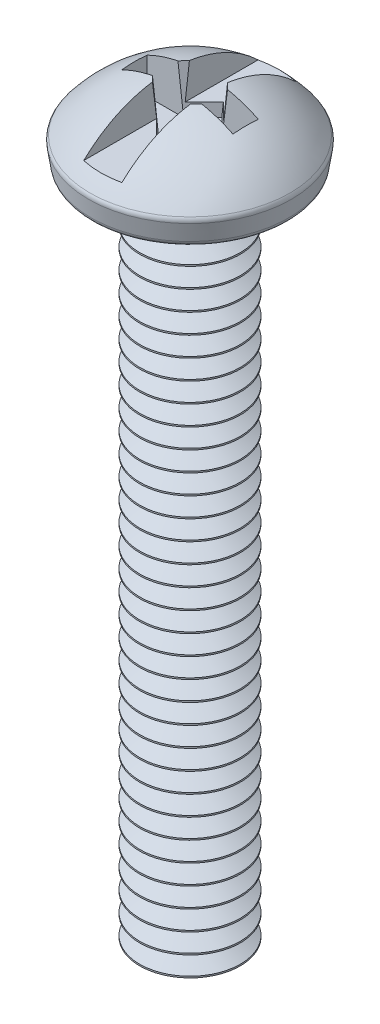
SolidWorks part; units mm, degrees
material "Plain Carbon Steel"
ref_plane "Front Plane" through (0, 0, 0) normal (0, 0, 1) x (1, 0, 0)
ref_plane "Top Plane" through (0, 0, 0) normal (0, 1, 0) x (1, 0, 0)
ref_plane "Right Plane" through (0, 0, 0) normal (1, 0, 0) x (0, 0, -1)
sketch "Sketch1" plane through (0, 0, 0) normal (0, 0, 1) x (1, 0, 0)
  line L0 (0, 3.048) -> (0, -26.9875)
  line L1 (0, 0) -> (2.0066, 0) construction
  line L2 (2.0066, 0) -> (2.0066, -26.9875)
  line L3 (2.0066, -26.9875) -> (0, -26.9875)
  line L4 (2.0066, 0) -> (3.6929, 0)
  line L5 (3.944, 0.2163) -> (4.048, 0.9093)
  line L6 (0, 3.048) -> (4.064, 3.048) construction
  line L7 (4.064, 3.048) -> (4.064, 1.016) construction
  arc A0 (0, 3.048) -> (3.9966, 1.1038) centre (0, -2.032) cw
  arc A1 (3.6929, 0) -> (3.944, 0.2163) centre (3.6929, 0.254) ccw
  arc A2 (4.048, 0.9093) -> (3.9966, 1.1038) centre (3.7968, 0.947) ccw
  point P10 (4.7481, 0)
  point P11 (3.9688, 0.9062)
  point P14 (3.9116, 0)
  dimension "D6" = 0.254
  dimension "D1" = 3.048
  dimension "D2" = 26.9875
  dimension "D3" = 4.064
  dimension "D4" = 3.9116
  dimension "D5" = 1.016
  dimension "D7" = 2.0066
revolve "Revolve1" add sketch "Sketch1" angle 360 about L0
sketch "Sketch2" plane through (0, 0, 0) normal (0, 0, 1) x (1, 0, 0)
  line L0 (0, 0) -> (0, -26.9875) construction
  line L1 (-2.0066, -26.9875) -> (2.0066, -26.9875) construction
  line L2 (0, -26.9875) -> (1.3716, -26.9875) construction
  line L3 (1.3716, -26.9875) -> (2.059, -26.9875) construction
  line L4 (2.059, -26.9875) -> (2.8528, -26.9875) construction
  line L5 (2.8528, -26.5906) -> (2.8528, -27.3844)
  line L6 (2.059, -26.5906) -> (2.059, -27.3844) construction
  line L7 (2.8528, -26.5906) -> (2.059, -26.5906)
  line L8 (2.059, -26.5906) -> (1.3716, -26.9875)
  line L9 (1.3716, -26.9875) -> (2.059, -27.3844)
  line L10 (2.059, -27.3844) -> (2.8528, -27.3844)
  point P12 (2.0598, -26.9875)
  point P14 (2.6993, -26.9875)
  point P15 (2.0448, -26.9875)
  dimension "D1" = 0.7937
  dimension "D2" = 60
  dimension "D3" = 1.3716
revolve "Cut-Revolve1" cut sketch "Sketch2" angle 360 about L0
pattern_linear "LPattern1" count 34 spacing 0.7937 along (0, 1, 0) of "Cut-Revolve1"
sketch "Sketch3" plane through (0, 0, 0) normal (0, 0, 1) x (1, 0, 0)
  line L0 (0, 0) -> (0, 1.5875) construction
  line L2 (-0.762, 4.1275) -> (0.762, 4.1275)
  line L3 (-0.762, 4.1275) -> (-0.762, 1.5875)
  line L4 (-0.762, 1.5875) -> (0.762, 1.5875)
  line L5 (0.762, 4.1275) -> (0.762, 1.5875)
  dimension "D1" = 1.5875
  dimension "D2" = 2.54
  dimension "D3" = 1.524
extrude "Cut-Extrude1" cut sketch "Sketch3" against normal through all both and the other way through all
sketch "Sketch4" plane through (0, 1.5875, 0) normal (0, 1, 0) x (1, 0, 0)
  line L1 (-2.2225, 0.508) -> (2.2225, 0.508)
  line L2 (-2.2225, 0.508) -> (-2.2225, -0.508)
  line L3 (-2.2225, -0.508) -> (2.2225, -0.508)
  line L4 (2.2225, 0.508) -> (2.2225, -0.508)
  line L5 (-2.2225, 0.508) -> (2.2225, -0.508) construction
  line L6 (-2.2225, -0.508) -> (2.2225, 0.508) construction
  point P0 (0, 0)
  dimension "D1" = 4.445
  dimension "D2" = 1.016
extrude "Cut-Extrude2" cut sketch "Sketch4" against normal blind 0.508 and the other way through all
sketch "Sketch5" plane through (0, 1.0795, 0) normal (0, 1, 0) x (1, 0, 0)
  line L1 (0, -1.27) -> (1.27, 0)
  line L2 (1.27, 0) -> (0, 1.27)
  line L3 (0, 1.27) -> (-1.27, 0)
  line L4 (-1.27, 0) -> (0, -1.27)
  circle A0 centre (0, 0) radius 0.898 construction
  point P1 (0, 1.2465)
  point P9 (0, 0)
extrude "Cut-Extrude3" cut sketch "Sketch5" along normal through all draft 5 draft outward yes
